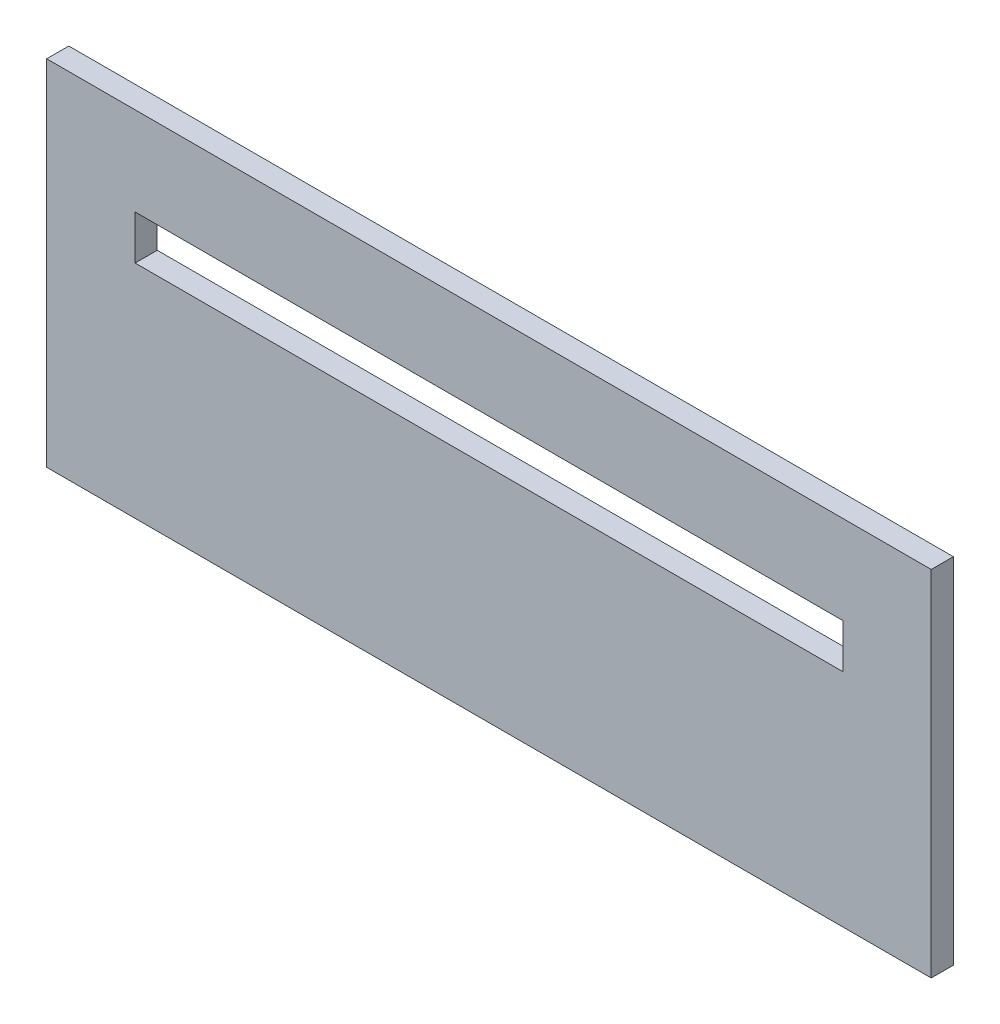
SolidWorks part; units mm, degrees
ref_plane "Front Plane" through (0, 0, 0) normal (0, 0, 1) x (1, 0, 0)
ref_plane "Top Plane" through (0, 0, 0) normal (0, 1, 0) x (1, 0, 0)
ref_plane "Right Plane" through (0, 0, 0) normal (1, 0, 0) x (0, 0, -1)
sketch "Sketch1" plane through (0, 0, 0) normal (0, 0, 1) x (1, 0, 0)
  line L1 (97.955, 41.8692) -> (-29.045, 41.8692)
  line L2 (97.955, 41.8692) -> (97.955, -8.9308)
  line L3 (97.955, -8.9308) -> (-29.045, -8.9308)
  line L4 (-29.045, 41.8692) -> (-29.045, -8.9308)
  dimension "D1" = 50.8
  dimension "D2" = 127
extrude "Boss-Extrude1" add sketch "Sketch1" along normal blind 3.175
sketch "Sketch2" plane through (0, 0, 3.175) normal (0, 0, 1) x (1, 0, 0)
  line L0 (97.955, 41.8692) -> (-29.045, 41.8692) construction
  line L1 (-16.345, 29.1692) -> (85.255, 29.1692)
  line L2 (-16.345, 29.1692) -> (-16.345, 22.8192)
  line L3 (-16.345, 22.8192) -> (85.255, 22.8192)
  line L4 (85.255, 29.1692) -> (85.255, 22.8192)
  line L5 (97.955, -8.9308) -> (97.955, 41.8692) construction
  dimension "D1" = 12.7
  dimension "D2" = 6.35
  dimension "D3" = 101.6
  dimension "D4" = 12.7
extrude "Cut-Extrude1" cut sketch "Sketch2" against normal blind 3.175
